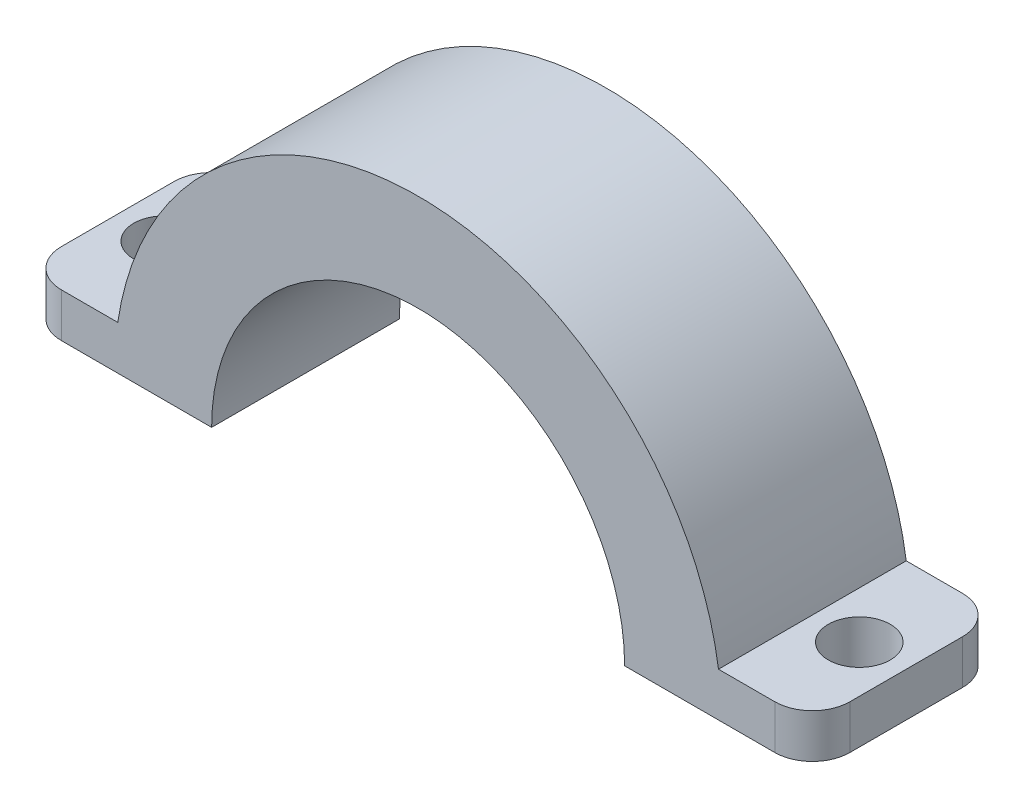
SolidWorks part; units mm, degrees
ref_plane "Plan de face" through (0, 0, 0) normal (0, 0, 1) x (1, 0, 0)
ref_plane "Plan de dessus" through (0, 0, 0) normal (0, 1, 0) x (1, 0, 0)
ref_plane "Plan de droite" through (0, 0, 0) normal (1, 0, 0) x (0, 0, -1)
sketch "Sketch1" plane through (0, 0, 0) normal (0, 0, 1) x (1, 0, 0)
  line L0 (-21, 0) -> (-11, 0)
  line L5 (0, 0) -> (-11, 0) construction
  line L11 (-16, 2.3437) -> (-21, 2.3437)
  line L12 (-21, 0) -> (-21, 2.3437)
  line L13 (0, 0) -> (0, 11) construction
  line L14 (-16, 0) -> (-16, 2.3437) construction
  line L15 (0, 11) -> (0, 16.1707)
  arc A2 (-11, 0) -> (0, 11) centre (0, 0) cw
  arc A3 (-16, 2.3437) -> (0, 16.1707) centre (0, 0) cw
  point P0 (0, 0)
  point P10 (0, 0)
  dimension "D1" = 11
  dimension "D2" = 10
  dimension "D3" = 11
  dimension "D4" = 5
extrude "Boss-Extrude1" add sketch "Sketch1" along normal blind 10
sketch "Sketch2" plane through (0, 2.3437, 0) normal (0, 1, 0) x (1, 0, 0)
  line L0 (-21, 0) -> (-16, -10) construction
  circle A0 centre (-18.5, -5) radius 1.65
  dimension "D1" = 3.3
extrude "Cut-Extrude1" cut sketch "Sketch2" against normal blind 10
fillet "Fillet1" radius 2 2 edges at (-21, 1.1719, 0) (-21, 1.1719, 10)
mirror "Mirror1" about plane through (0, 11, 10) normal (-1, 0, 0) of "Cut-Extrude1", "Fillet1", "Boss-Extrude1"
